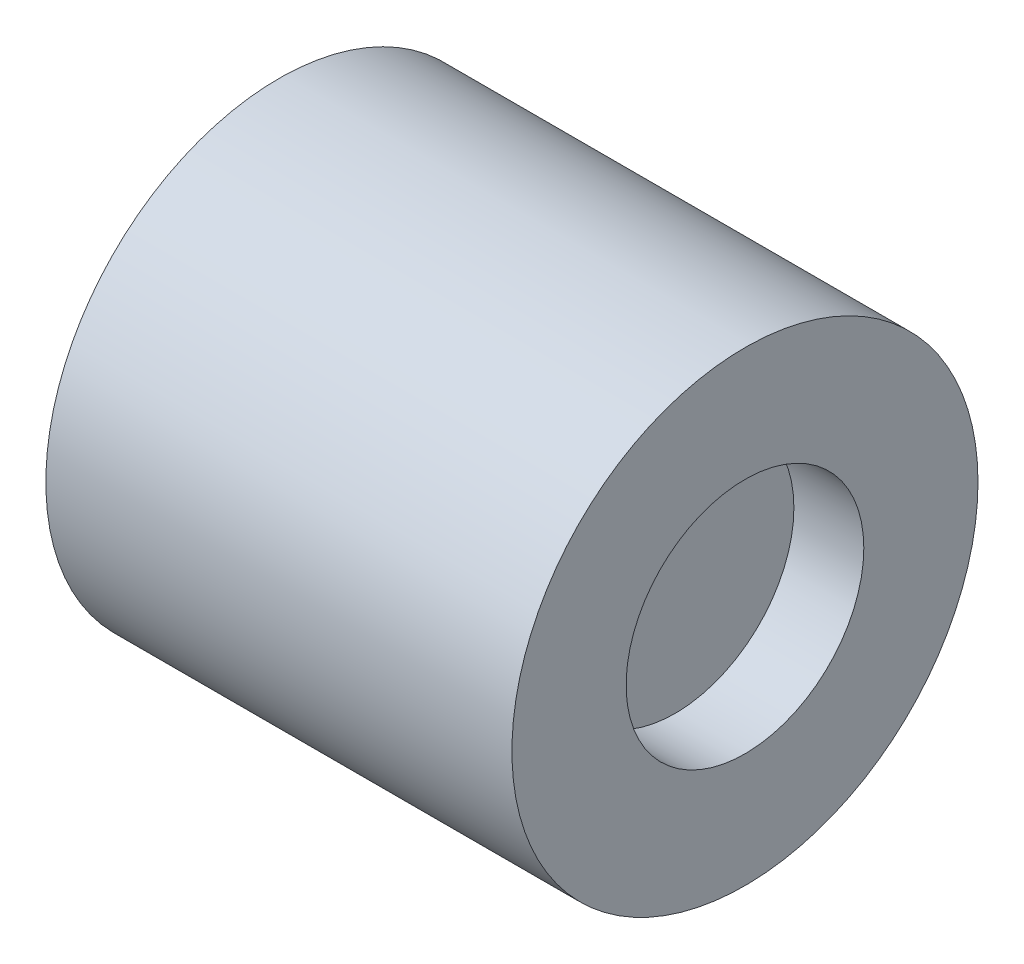
SolidWorks part; units mm, degrees
ref_plane "Front Plane" through (0, 0, 0) normal (1, 0, 0) x (0, 1, 0)
ref_plane "Top Plane" through (0, 0, 0) normal (0, 0, 1) x (0, 1, 0)
ref_plane "Right Plane" through (0, 0, 0) normal (0, 1, 0) x (-1, 0, 0)
sketch "Sketch1" plane through (0, 0, 0) normal (1, 0, 0) x (0, 1, 0)
  circle A0 centre (0, 0) radius 5
  dimension "D1" = 10
extrude "Boss-Extrude1" add sketch "Sketch1" along normal blind 10
sketch "Sketch2" plane through (10, 0, 0) normal (1, 0, 0) x (0, 1, 0)
  circle A0 centre (0, 0) radius 2.55
  dimension "D1" = 5.1
extrude "Cut-Extrude1" cut sketch "Sketch2" against normal blind 1.5
sketch "Sketch4" plane through (0, 0, 0) normal (-1, 0, 0) x (0, -1, 0)
  circle A0 centre (0, 0) radius 2.525
  dimension "D1" = 5.05
extrude "Cut-Extrude2" cut sketch "Sketch4" against normal blind 6
